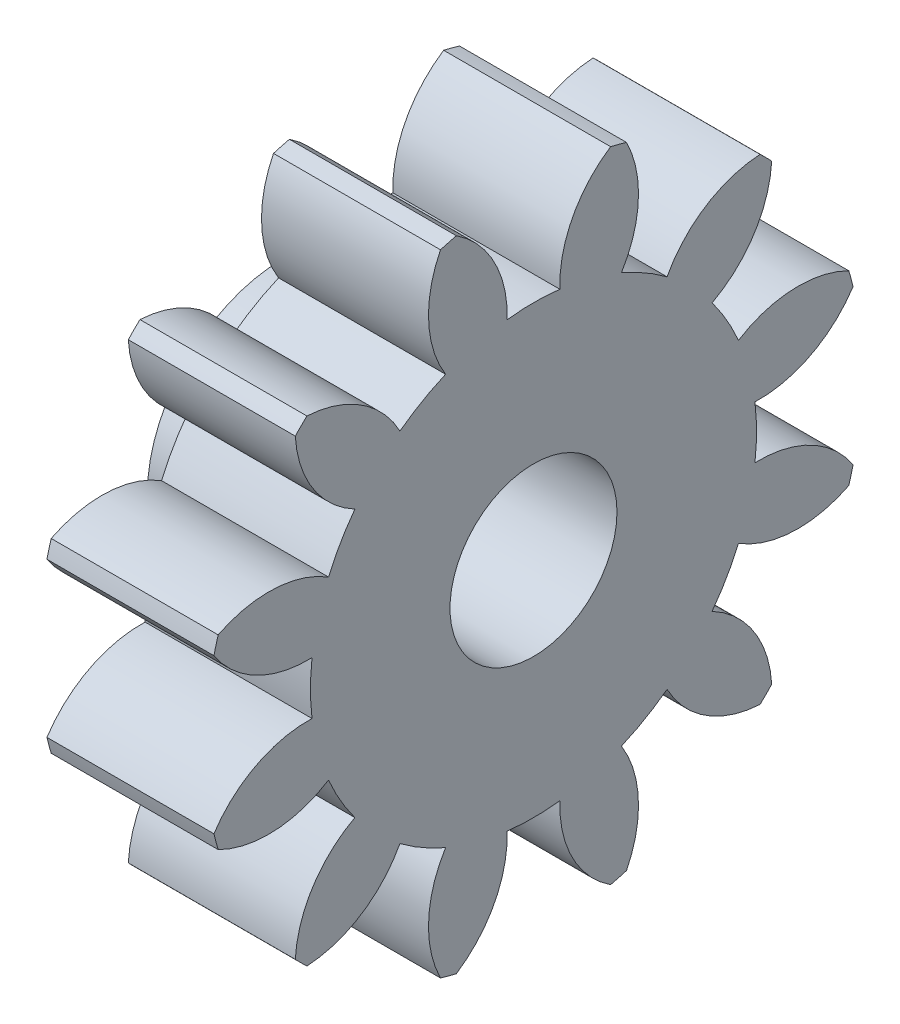
SolidWorks part; units mm, degrees
material "PLA"
ref_plane "Plane1" through (0, 0, 0) normal (0, 0, 1) x (1, 0, 0)
ref_plane "Plane2" through (0, 0, 0) normal (0, 1, 0) x (1, 0, 0)
ref_plane "Plane3" through (0, 0, 0) normal (1, 0, 0) x (0, 0, -1)
other "Configuration Table"
sketch "HoldingSke" plane through (0, 0, 0) normal (0, 1, 0) x (1, 0, 0)
  line L0 (0, 0) -> (0.8695, -0.1848)
  line L1 (-15, 0) -> (100, 0) construction
  line L2 (0, 0) -> (-2.1039, 2.3779)
  line L3 (0, 0) -> (-11.863, 4.5341)
  line L4 (0, 0) -> (8.4473, 1.7955)
  line L5 (0, 0) -> (-46.8476, -17.4728)
  line L6 (0, 0) -> (-3.3159, -2.2372)
  line L7 (-2.1039, 2.3779) -> (8.6586, 51.2059)
  line L8 (-76.2, 54.61) -> (-75.7, 54.61)
  line L9 (-71.009, 38.7566) -> (-53.1078, 45.2721)
  line L10 (-76.2, 71.12) -> (104.1128, 71.12)
  line L11 (0, 0) -> (-4, 0)
  line L12 (-76.2, 101.6) -> (-76.158, 101.6)
  line L13 (24.9733, 27.94) -> (52.9518, 28.4284)
  line L14 (24.9733, 27.94) -> (24.9743, 27.94)
  line L15 (24.9733, 27.94) -> (100.4006, 29.5858)
  line L16 (-63.627, -1.125) -> (-12.827, -1.125)
  circle A0 centre (0, 0) radius 1.5
  circle A1 centre (0, 0) radius 5.3427
  circle A2 centre (0, 0) radius 37.5
  circle A3 centre (0, 0) radius 1.5
  dimension "MHD" = 10.6855
  dimension "Hub_dia" = 75
  dimension "Bore" = 3
  dimension "MBD" = 3
  dimension "Num_teeth" = 12
  dimension "Pitch" = 0.8889
  dimension "Overall_len" = 50
  dimension "Show_teeth" = 12
  dimension "Thickness" = 4
  dimension "OAL" = 50.0001
  dimension "T_dim" = 0.5
  dimension "Ap" = 20
  dimension "H" = 19.05
  dimension "Pitch_radius" = 180.3128
  dimension "Width" = 4
  dimension "Backlash" = 0.042
  dimension "Addendum_fac" = 1
  dimension "Dedendum_fac" = 1.25
  dimension "Clearance_fac" = 0.25
  dimension "Dedendum_add" = 0.001
  dimension "Module" = 1.125
sketch "BasProSke" plane through (0, 0, 0) normal (0, 1, 0) x (1, 0, 0)
  line L0 (-10, 0) -> (60, 0) construction
  line L1 (0, 0) -> (0, 7.875)
  line L2 (0, 0) -> (4, 0)
  line L3 (4, 0) -> (4, 7.875)
  line L4 (4, 7.875) -> (0, 7.875)
  dimension "Thickness" = 4
  dimension "Diameter" = 15.75
revolve "Base-Revolve" add sketch "BasProSke" angle 360 about L0
sketch "TooCutSke" plane through (0, 0, 0) normal (1, 0, 0) x (0, 0, -1)
  line L1 (0, 0) -> (0, 107) construction
  line L2 (0, 0) -> (-0.9544, 6.6822) construction
  line L3 (0, 0) -> (-3.469, 12.9463) construction
  line L4 (-0.9544, 6.6822) -> (-1.7345, 6.4732) construction
  arc A0 (0.6314, 5.3053) -> (-0.6314, 5.3053) centre (0, 0) ccw
  arc A1 (1.8767, 7.6743) -> (-1.8767, 7.6743) centre (0, 0) ccw
  circle A2 centre (0, 0) radius 6.75 construction
  circle A3 centre (0, 0) radius 6.3429 construction
  arc A4 (-0.6314, 5.3053) -> (-1.8767, 7.6743) centre (-3.3298, 5.3986) ccw
  arc A5 (1.8767, 7.6743) -> (0.6314, 5.3053) centre (3.3298, 5.3986) ccw
  dimension "Root_dia" = 10.6855
  dimension "Overcut_dia" = 15.8008
  dimension "Pitch_dia" = 13.5
  dimension "Base_dia" = 12.6859
  dimension "Flank_rad" = 2.7
  dimension "Half_ang" = 15
  dimension "Half_CT" = 0.8076
extrude "ToothCut" cut sketch "TooCutSke" along normal through all
fillet "Breaks" [suppressed] radius 0.0225
fillet "RootFillets" [suppressed] radius 0.2823
pattern_circular "TeethCuts" count 12 every 30 about axis through (-10, 0, 0) along (1, 0, 0) of "ToothCut", "RootFillets", "Breaks"
sketch "HubNeaOneSke" plane through (0, 0, 0) normal (-1, 0, 0) x (0, 0, 1)
  circle A0 centre (0, 0) radius 5.3427
  dimension "Diameter" = 10.6855
extrude "HubNearOne" [suppressed] add sketch "HubNeaOneSke" along normal blind 46.0001
sketch "HubNeaBotSke" plane through (0, 0, 0) normal (-1, 0, 0) x (0, 0, 1)
  circle A0 centre (0, 0) radius 5.3427
  dimension "Diameter" = 10.6855
extrude "HubNearBoth" [suppressed] add sketch "HubNeaBotSke" along normal blind 23
ref_plane "FarPln" through (4, 0, 0) normal (1, 0, 0) x (0, 0, -1)
sketch "HubFarSke" plane through (4, 0, 0) normal (1, 0, 0) x (0, 0, -1)
  circle A0 centre (0, 0) radius 5.3427
  dimension "Diameter" = 10.6855
extrude "HubFar" [suppressed] add sketch "HubFarSke" along normal blind 23
sketch "BorSke" plane through (0, 0, 0) normal (1, 0, 0) x (0, 0, -1)
  circle A0 centre (0, 0) radius 1
  dimension "Diameter" = 2
extrude "Bore" cut sketch "BorSke" along normal mid plane 100.0001
sketch "KeySke" plane through (0, 0, 0) normal (1, 0, 0) x (0, 0, -1)
  line L0 (-0.6, 0) -> (-0.6, 2)
  line L1 (-0.6, 2) -> (0.6, 2)
  line L2 (0.6, 2) -> (0.6, 0)
  line L3 (0, 0) -> (0, 34) construction
  line L4 (-0.6, 0) -> (0.6, 0)
  dimension "Offset" = 2
  dimension "Width" = 1.2
extrude "Keyway" [suppressed] cut sketch "KeySke" along normal mid plane 100.0001
pattern_circular "Keyway2" [suppressed] count 2 every 90 about axis through (-10, 0, 0) along (1, 0, 0)
sketch "Sketch1" plane through (0, 0, 0) normal (-1, 0, 0) x (0, 0, 1)
  circle A0 centre (0, 0) radius 2.25
  circle A1 centre (0, 0) radius 3.25
  dimension "D1" = 4.5
  dimension "D2" = 1
extrude "Boss-Extrude1" add sketch "Sketch1" along normal blind 2
sketch "Sketch2" plane through (4, 0, 0) normal (1, 0, 0) x (0, 0, -1)
  circle A0 centre (0, 0) radius 2
  dimension "D1" = 4
extrude "Cut-Extrude1" cut sketch "Sketch2" against normal offset from surface (3 mm away) 3 up to face at (-2, 0, 3.25)
equation "' \"Module@HoldingSke\" = 6.35"
equation "' \"Num_teeth@HoldingSke\" = 12"
equation "' \"Ap@HoldingSke\" =  20"
equation "' \"Ap@HoldingSke\" = 20"
equation "' \"Width@HoldingSke\" = 0.5 * 25.4"
equation "' \"Hub_dia@HoldingSke\"= 1 * 25.4"
equation "' \"Hub_dia@HoldingSke\" = 1 * 25.4"
equation "' \"Overall_len@HoldingSke\" = 1.0 * 25.4"
equation "' \"Bore@HoldingSke\" = 0.75 * 25.4"
equation "' \"T_dim@HoldingSke\" = 0.1 * 25.4"
equation "' \"Width@KeySke\" = 0.25 * 25.4"
equation "' \"Show_teeth@HoldingSke\" = 13"
equation "' \"Backlash@HoldingSke\" = 0.009 * 25.4"
equation "' \"Addendum_fac@HoldingSke\" = 1.0"
equation "' \"Dedendum_fac@HoldingSke\" = 1.25"
equation "' \"Dedendum_add@HoldingSke\" = 0.00005 * 25.4"
equation "' \"Clearance_fac@HoldingSke\" = 0.25"
equation "\"Pitch@HoldingSke\" = 1 / \"Module@HoldingSke\""
equation "\"Overcut_dia@TooCutSke\" = (\"Num_teeth@HoldingSke\" + 2 * \"Addendum_fac@HoldingSke\") / \"Pitch@HoldingSke\" + 0.002 * 25.4"
equation "\"Pitch_dia@TooCutSke\" = \"Num_teeth@HoldingSke\" / \"Pitch@HoldingSke\""
equation "\"Base_dia@TooCutSke\" = \"Num_teeth@HoldingSke\" / \"Pitch@HoldingSke\" * cos((\"Ap@HoldingSke\"  * 3.14159265 / 180))"
equation "\"Root_dia@TooCutSke\" = (\"Num_teeth@HoldingSke\" + 2) / \"Pitch@HoldingSke\" - 2 * (\"Addendum_fac@HoldingSke\" + \"Dedendum_fac@HoldingSke\") / \"Pitch@HoldingSke\" - \"Dedendum_add@HoldingSke\" * 2"
equation "\"Half_ang@TooCutSke\" = 180 / \"Num_teeth@HoldingSke\""
equation "\"Half_CT@TooCutSke\" = \"Num_teeth@HoldingSke\" / \"Pitch@HoldingSke\" * sin((3.14159265 / 2 / \"Num_teeth@HoldingSke\")) / 2 - 7 * \"Backlash@HoldingSke\" / 4"
equation "\"Flank_rad@TooCutSke\" = \"Num_teeth@HoldingSke\" / \"Pitch@HoldingSke\" / 5"
equation "\"Radius@RootFillets\" = \"Clearance_fac@HoldingSke\" / \"Pitch@HoldingSke\" + \"Dedendum_add@HoldingSke\""
equation "\"Break_rad@Breaks\" = 0.02 / \"Pitch@HoldingSke\""
equation "\"Thickness@HoldingSke\" = \"Width@HoldingSke\""
equation "\"OAL@HoldingSke\" = \"Thickness@HoldingSke\""
equation "\"MHD@HoldingSke\" = (\"Num_teeth@HoldingSke\" + 2) / \"Pitch@HoldingSke\" - 2 * (\"Addendum_fac@HoldingSke\" + \"Dedendum_fac@HoldingSke\")  / \"Pitch@HoldingSke\" - \"Dedendum_add@HoldingSke\" * 2"
equation "\"MBD@HoldingSke\" = (\"Num_teeth@HoldingSke\" + 2) / \"Pitch@HoldingSke\" - 2 * (\"Addendum_fac@HoldingSke\" + \"Dedendum_fac@HoldingSke\")  / \"Pitch@HoldingSke\" - \"Dedendum_add@HoldingSke\" * 2 - 0.002 * 25.4"
equation "\"MHD@HoldingSke\" = ((sgn( \"MHD@HoldingSke\" - \"Hub_dia@HoldingSke\" )-1)*( \"MHD@HoldingSke\" - \"Hub_dia@HoldingSke\" ))/-2+ \"Hub_dia@HoldingSke\""
equation "\"MBD@HoldingSke\" = ((sgn( \"MBD@HoldingSke\" - \"Bore@HoldingSke\" )-1)*( \"MBD@HoldingSke\" - \"Bore@HoldingSke\" ))/-2+ \"Bore@HoldingSke\""
equation "\"OAL@HoldingSke\" = ((sgn( \"OAL@HoldingSke\" - \"Overall_len@HoldingSke\" )+1)*( \"OAL@HoldingSke\" - \"Overall_len@HoldingSke\" ))/2 + \"Overall_len@HoldingSke\" + 0.000002 * 25.4"
equation "\"Num_teeth@TeethCuts\" = int( \"Show_teeth@HoldingSke\" ) + 1"
equation "\"Num_teeth@TeethCuts\" = ((sgn( \"Num_teeth@TeethCuts\" - \"Num_teeth@HoldingSke\" )-1)*( \"Num_teeth@TeethCuts\" - \"Num_teeth@HoldingSke\" ))/-2+ \"Num_teeth@HoldingSke\""
equation "\"Num_teeth@TeethCuts\" = ((sgn( \"Num_teeth@TeethCuts\" - 2.0)+1)*( \"Num_teeth@TeethCuts\" - 2.0))/2 +2.0"
equation "\"Angle@TeethCuts\" = 360.0 / \"Num_teeth@HoldingSke\""
equation "\"Diameter@BasProSke\" = (\"Num_teeth@HoldingSke\" + 2 * \"Addendum_fac@HoldingSke\") / \"Pitch@HoldingSke\""
equation "\"Thickness@BasProSke\"  = \"Thickness@HoldingSke\""
equation "' \"Fillet_rad@BasProSke\" =  \"Thickness@HoldingSke\" * 0.05"
equation "' \"Fillet_rad@BasProSke\" = \"Thickness@HoldingSke\" * 0.05"
equation "\"MHD@HoldingSke\" = ((sgn( \"MHD@HoldingSke\" - \"Root_dia@TooCutSke\" )-1)*( \"MHD@HoldingSke\" - \"Root_dia@TooCutSke\" ))/-2+ \"Root_dia@TooCutSke\""
equation "\"Diameter@HubNeaOneSke\" = \"MHD@HoldingSke\""
equation "\"Length@HubNearOne\" = \"OAL@HoldingSke\" - \"Thickness@BasProSke\""
equation "\"Diameter@HubNeaBotSke\" = \"MHD@HoldingSke\""
equation "\"Length@HubNearBoth\" = ( \"OAL@HoldingSke\" - \"Thickness@BasProSke\" ) / 2.0"
equation "\"Thickness@FarPln\" = \"Thickness@BasProSke\""
equation "\"Diameter@HubFarSke\" = \"MHD@HoldingSke\""
equation "\"Length@HubFar\" = ( \"OAL@HoldingSke\" - \"Thickness@BasProSke\" ) / 2.0"
equation "\"D1@Bore\" = \"OAL@HoldingSke\" * 2.0"
equation "\"D1@Keyway\" = \"OAL@HoldingSke\" * 2.0"
equation "\"Offset@KeySke\" = \"T_dim@HoldingSke\" + \"MBD@HoldingSke\" / 2.0"
